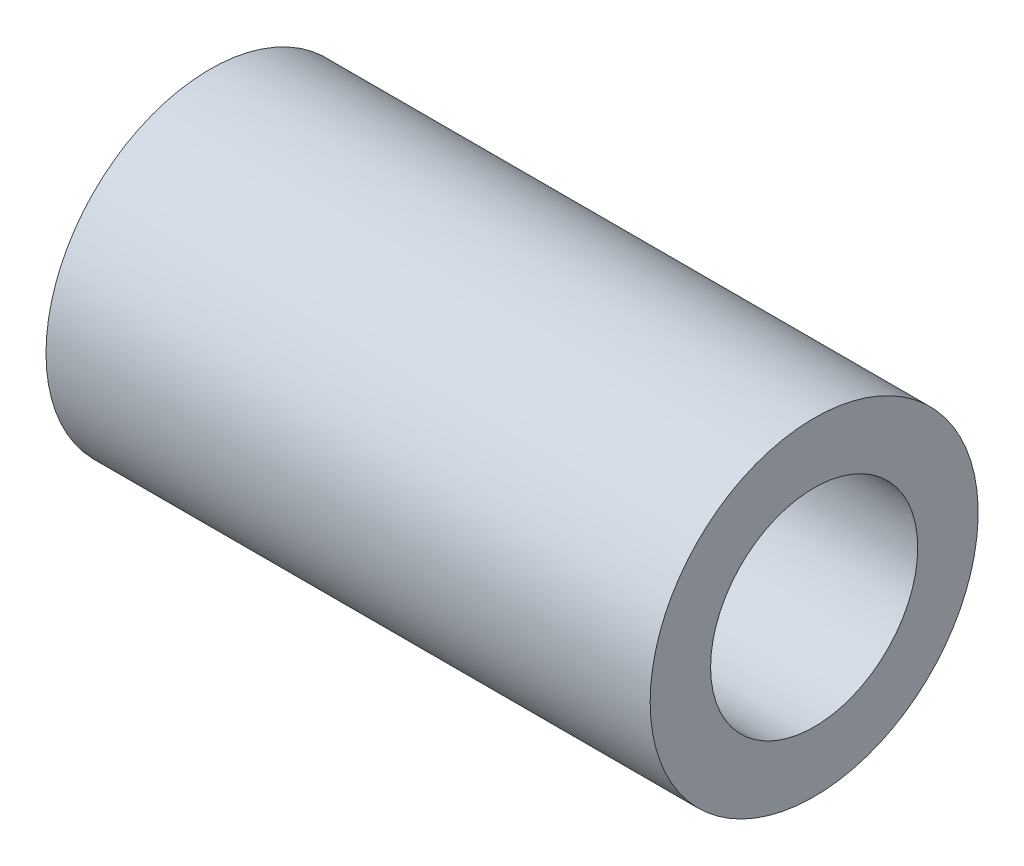
SolidWorks part; units mm, degrees
ref_plane "Plano frontal" through (0, 0, 0) normal (0, 0, 1) x (1, 0, 0)
ref_plane "Plano superior" through (0, 0, 0) normal (0, 1, 0) x (1, 0, 0)
ref_plane "Plano direito" through (0, 0, 0) normal (1, 0, 0) x (0, 0, -1)
ref_plane "Plano1" through (0, 0, 0) normal (0, 0, 1) x (1, 0, 0)
sketch "Esboço1" plane through (0, 0, 0) normal (0, 0, 1) x (1, 0, 0)
  line L0 (0, 9.525) -> (55.5625, 9.525)
  line L1 (55.5625, 9.525) -> (55.5625, 15.0812)
  line L2 (55.5625, 15.0812) -> (0, 15.0812)
  line L3 (0, 15.0812) -> (0, 9.525)
  line L4 (55.5625, 0) -> (0, 0) construction
revolve "Revolução1" add sketch "Esboço1" angle 360 about L4
